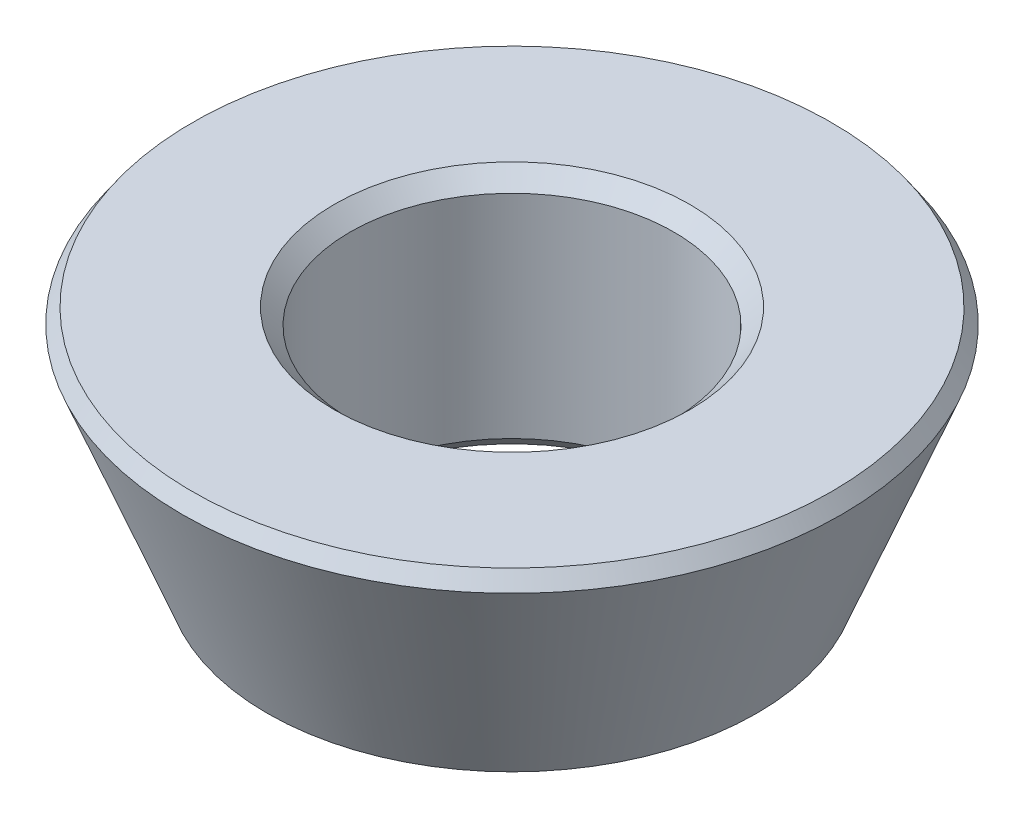
SolidWorks part; units mm, degrees
ref_plane "Front Plane" through (0, 0, 0) normal (0, 0, 1) x (1, 0, 0)
ref_plane "Top Plane" through (0, 0, 0) normal (0, 1, 0) x (1, 0, 0)
ref_plane "Right Plane" through (0, 0, 0) normal (1, 0, 0) x (0, 0, -1)
sketch "Sketch3" plane through (0, 0, 0) normal (0, 0, 1) x (1, 0, 0)
  line L0 (0, 0) -> (4.5, 0)
  line L1 (4.5, 0) -> (6.3198, 4.6)
  line L2 (6.3198, 4.6) -> (0, 4.6)
  line L3 (0, 4.6) -> (0, 0)
  line L4 (3.05, 4.6) -> (3.05, 0)
  dimension "D1" = 4.6
  dimension "D2" = 6.3198
  dimension "D3" = 3.05
  dimension "D4" = 4.5
revolve "Revolve1" add sketch "Sketch3" angle 360 about L3
chamfer "Chamfer3" distance 0.3 distance2 0.3 4 edges at (-3.05, 4.6, 0) (-3.05, 0, 0) (-4.5, 0, 0) (-6.3198, 4.6, 0)
